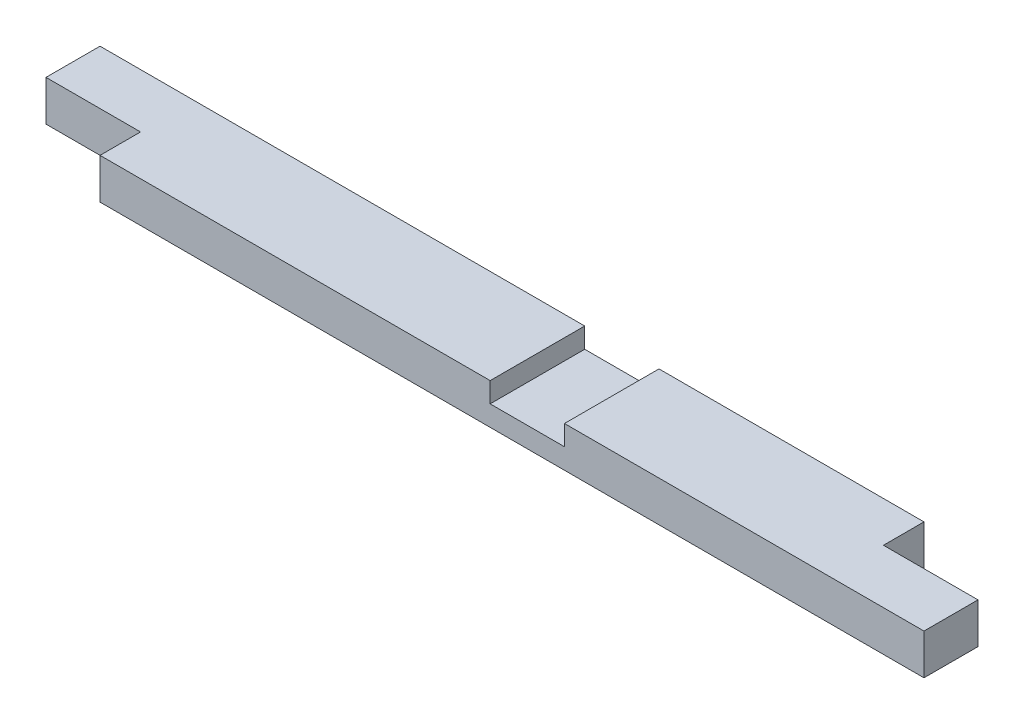
SolidWorks part; units mm, degrees
material "Pine"
ref_plane "Front Plane" through (0, 0, 0) normal (0, 0, 1) x (1, 0, 0)
ref_plane "Top Plane" through (0, 0, 0) normal (0, 1, 0) x (1, 0, 0)
ref_plane "Right Plane" through (0, 0, 0) normal (1, 0, 0) x (0, 0, -1)
sketch "Sketch1" plane through (0, 0, 0) normal (0, 1, 0) x (1, 0, 0)
  line L1 (0, 0) -> (863.6, 0)
  line L2 (0, 0) -> (0, 88.9)
  line L3 (0, 88.9) -> (863.6, 88.9)
  line L4 (863.6, 0) -> (863.6, 88.9)
  dimension "D1" = 88.9
  dimension "D2" = 863.6
extrude "Boss-Extrude1" add sketch "Sketch1" along normal blind 38.1
sketch "Sketch2" plane through (0, 0, 0) normal (0, -1, 0) x (1, 0, 0)
  line L0 (863.6, -88.9) -> (0, -88.9) construction
  line L1 (863.6, -50.8) -> (774.7, -50.8)
  line L2 (863.6, -88.9) -> (863.6, -50.8)
  line L4 (774.7, -88.9) -> (774.7, -50.8)
  line L5 (863.6, -88.9) -> (774.7, -88.9)
  line L7 (863.6, 0) -> (863.6, -88.9) construction
  line L8 (0, 0) -> (863.6, 0) construction
  dimension "D1" = 88.9
  dimension "D2" = 50.8
sketch "Sketch3" plane through (0, 38.1, 0) normal (0, 1, 0) x (1, 0, 0)
  line L1 (0, 0) -> (88.9, 0)
  line L2 (0, 0) -> (0, 38.1)
  line L3 (0, 38.1) -> (88.9, 38.1)
  line L4 (88.9, 0) -> (88.9, 38.1)
  dimension "D1" = 88.9
  dimension "D2" = 38.1
extrude "Cut-Extrude2" cut sketch "Sketch3" against normal through all
extrude "Cut-Extrude3" cut sketch "Sketch2" against normal through all
sketch "Sketch4" plane through (0, 0, -88.9) normal (0, 0, -1) x (-1, 0, 0)
  line L0 (-774.7, 38.1) -> (0, 38.1) construction
  line L1 (-525.5736, 19.1545) -> (-455.7236, 19.1545)
  line L2 (-525.5736, 19.1545) -> (-525.5736, 38.1)
  line L3 (-525.5736, 38.1) -> (-455.7236, 38.1)
  line L4 (-455.7236, 19.1545) -> (-455.7236, 38.1)
  dimension "D1" = 19.1545
  dimension "D2" = 455.7236
  dimension "D3" = 69.85
extrude "Cut-Extrude4" cut sketch "Sketch4" against normal through all
